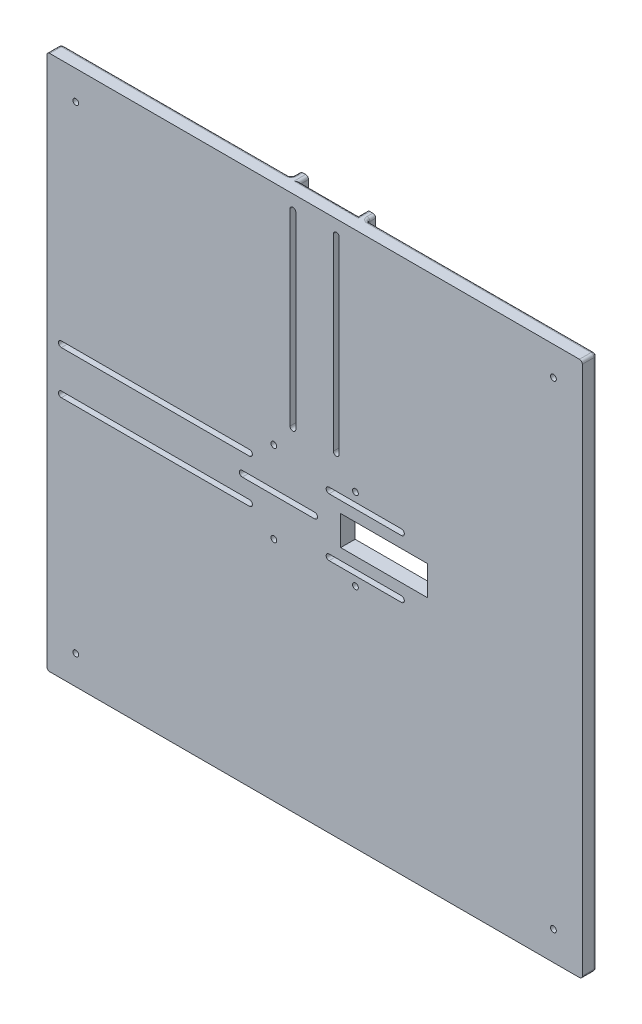
SolidWorks part; units mm, degrees
ref_plane "Plan de face" through (0, 0, 0) normal (0, 0, 1) x (1, 0, 0)
ref_plane "Plan de dessus" through (0, 0, 0) normal (0, 1, 0) x (1, 0, 0)
ref_plane "Plan de droite" through (0, 0, 0) normal (1, 0, 0) x (0, 0, -1)
sketch "Esquisse1" plane through (0, 0, 0) normal (0, 0, 1) x (1, 0, 0)
  line L1 (-92.5, 92.5) -> (92.5, 92.5)
  line L2 (-92.5, 92.5) -> (-92.5, -92.5)
  line L3 (-92.5, -92.5) -> (92.5, -92.5)
  line L4 (92.5, 92.5) -> (92.5, -92.5)
  dimension "D1" = 185
  dimension "D2" = 185
  dimension "D3" = 92.5
  dimension "D4" = 92.5
extrude "Boss.-Extru.1" add sketch "Esquisse1" along normal blind 5
sketch "Esquisse2" plane through (0, 0, 0) normal (0, 0, -1) x (-1, 0, 0)
  line L1 (22.5, 10.1) -> (92.5, 10.1)
  line L4 (92.5, 10.1) -> (92.5, 13.1)
  line L5 (92.5, -13.1) -> (22.5, -13.1)
  line L6 (92.5, -13.1) -> (92.5, -10.1)
  line L7 (92.5, -10.1) -> (22.5, -10.1)
  line L19 (92.5, 92.5) -> (92.5, -92.5) construction
  line L24 (13.1, 22.5) -> (13.1, 92.5)
  line L25 (-92.5, 92.5) -> (92.5, 92.5) construction
  line L26 (10.1, 22.5) -> (10.1, 92.5)
  line L28 (-13.1, 92.5) -> (-10.1, 92.5)
  line L29 (10.1, 92.5) -> (13.1, 92.5)
  line L31 (-10.1, 92.5) -> (-10.1, 22.5)
  line L32 (-13.1, 92.5) -> (-13.1, 22.5)
  line L33 (-10.1, 22.5) -> (-13.1, 22.5)
  line L35 (22.5, -10.1) -> (22.5, -13.1)
  line L36 (92.5, 13.1) -> (22.5, 13.1)
  line L37 (22.5, 13.1) -> (22.5, 10.1)
  line L38 (13.1, 22.5) -> (10.1, 22.5)
  dimension "D1" = 20.2
  dimension "D2" = 3
  dimension "D3" = 3
  dimension "D4" = 10.1
  dimension "D5" = 3
  dimension "D6" = 3
  dimension "D7" = 20.2
  dimension "D8" = 10.1
  dimension "D9" = 70
  dimension "D10" = 70
extrude "Boss.-Extru.2" add sketch "Esquisse2" along normal blind 3
fillet "Congé1" radius 1 32 edges at (-13.1, 57.5, 0) (-57.5, -13.1, 0) (-13.1, 92.5, -1.5) (-92.5, -13.1, -1.5) (92.5, -92.5, 2.5) (92.5, 92.5, 2.5) (92.5, 0, 0) (0, 92.5, 0) (-92.5, 0, 0) (-52.8, 92.5, 0) (-92.5, 52.8, 0) (-92.5, 92.5, 2.5) (52.8, 92.5, 0) (0, -92.5, 0) (-92.5, -52.8, 0) (-92.5, -92.5, 2.5) (-10.1, 92.5, -1.5) (-92.5, 10.1, -1.5) (-92.5, -10.1, -1.5) (13.1, 92.5, -1.5) (10.1, 92.5, -1.5) (13.1, 57.5, 0) (-92.5, 13.1, -1.5) (-57.5, 13.1, 0) (-22.5, -11.6, 0) (11.6, 22.5, 0) (-11.6, 22.5, 0) (-22.5, 11.6, 0) (-22.5, -13.1, -1.5) (13.1, 22.5, -1.5) (-13.1, 22.5, -1.5) (-22.5, 13.1, -1.5)
sketch "Esquisse4" plane through (0, 0, 0) normal (0, 0, -1) x (-1, 0, 0)
  line L4 (-92.5, -91.5) -> (-92.5, 91.5) construction
  line L5 (91.5, -92.5) -> (-91.5, -92.5) construction
  line L6 (-91.5, 92.5) -> (-14.1, 92.5) construction
  line L7 (92.5, -14.1) -> (92.5, -91.5) construction
  circle A0 centre (-14.1, 14.1) radius 1
  circle A1 centre (14.1, 14.1) radius 1
  circle A2 centre (14.1, -14.1) radius 1
  circle A3 centre (-14.1, -14.1) radius 1
  circle A4 centre (-82.5, -82.5) radius 1
  circle A5 centre (-82.5, 82.5) radius 1
  circle A6 centre (82.5, -82.5) radius 1
  circle A7 centre (82.5, 82.5) radius 1
  dimension "D1" = 2
  dimension "D4" = 4
  dimension "D5" = 4
  dimension "D6" = 10
  dimension "D7" = 10
  dimension "D8" = 10
  dimension "D9" = 10
  dimension "D10" = 4
  dimension "D11" = 4
extrude "Enlèv. mat.-Extru.1" cut sketch "Esquisse4" against normal up to next
sketch "Esquisse5" plane through (0, 0, 0) normal (0, 0, -1) x (-1, 0, 0)
  line L0 (-7.5, 87.5) -> (-7.5, 22.5) construction
  line L1 (-6.5, 87.5) -> (-6.5, 22.5)
  line L2 (-8.5, 87.5) -> (-8.5, 22.5)
  line L3 (7.5, 87.5) -> (7.5, 22.5) construction
  line L4 (8.5, 87.5) -> (8.5, 22.5)
  line L5 (6.5, 87.5) -> (6.5, 22.5)
  line L9 (10.1, 91.5) -> (10.1, 21.5) construction
  line L10 (-10.1, 92.5) -> (10.1, 92.5) construction
  line L11 (-10.1, 21.5) -> (-10.1, 91.5) construction
  line L12 (-91.5, 92.5) -> (-14.1, 92.5) construction
  arc A0 (-6.5, 87.5) -> (-8.5, 87.5) centre (-7.5, 87.5) ccw
  arc A1 (-8.5, 22.5) -> (-6.5, 22.5) centre (-7.5, 22.5) ccw
  arc A2 (8.5, 87.5) -> (6.5, 87.5) centre (7.5, 87.5) ccw
  arc A3 (6.5, 22.5) -> (8.5, 22.5) centre (7.5, 22.5) ccw
  point P2 (-7.5, 55)
  point P7 (7.5, 55)
  dimension "D1" = 1
  dimension "D2" = 1
  dimension "D3" = 2.6
  dimension "D4" = 5
  dimension "D6" = 2.6
  dimension "D7" = 70
extrude "Enlèv. mat.-Extru.2" cut sketch "Esquisse5" against normal through all
sketch "Esquisse6" plane through (0, 0, 0) normal (0, 0, -1) x (-1, 0, 0)
  line L0 (87.5, -7.5) -> (22.5, -7.5) construction
  line L1 (87.5, -8.5) -> (22.5, -8.5)
  line L2 (87.5, -6.5) -> (22.5, -6.5)
  line L3 (22.5, 7.5) -> (87.5, 7.5) construction
  line L4 (22.5, 8.5) -> (87.5, 8.5)
  line L5 (22.5, 6.5) -> (87.5, 6.5)
  line L6 (91.5, -10.1) -> (21.5, -10.1) construction
  line L7 (21.5, 10.1) -> (91.5, 10.1) construction
  line L8 (92.5, 10.1) -> (92.5, -10.1) construction
  arc A0 (87.5, -8.5) -> (87.5, -6.5) centre (87.5, -7.5) ccw
  arc A1 (22.5, -6.5) -> (22.5, -8.5) centre (22.5, -7.5) ccw
  arc A2 (22.5, 8.5) -> (22.5, 6.5) centre (22.5, 7.5) ccw
  arc A3 (87.5, 6.5) -> (87.5, 8.5) centre (87.5, 7.5) ccw
  point P2 (55, -7.5)
  point P7 (55, 7.5)
  dimension "D1" = 1
  dimension "D2" = 1
  dimension "D3" = 2.6
  dimension "D4" = 2.6
  dimension "D5" = 5
  dimension "D7" = 70
extrude "Enlèv. mat.-Extru.3" cut sketch "Esquisse6" against normal up to next
sketch "Esquisse9" plane through (0, 0, 5) normal (0, 0, 1) x (1, 0, 0)
  line L0 (-25, 0) -> (0, 0) construction
  line L1 (-25, 1) -> (0, 1)
  line L2 (-25, -1) -> (0, -1)
  line L3 (5, 10) -> (30, 10) construction
  line L4 (5, 11) -> (30, 11)
  line L5 (5, 9) -> (30, 9)
  line L6 (5, -10) -> (30, -10) construction
  line L7 (5, -9) -> (30, -9)
  line L8 (5, -11) -> (30, -11)
  arc A0 (-25, 1) -> (-25, -1) centre (-25, 0) ccw
  arc A1 (0, -1) -> (0, 1) centre (0, 0) ccw
  arc A2 (5, 11) -> (5, 9) centre (5, 10) ccw
  arc A3 (30, 9) -> (30, 11) centre (30, 10) ccw
  arc A4 (5, -9) -> (5, -11) centre (5, -10) ccw
  arc A5 (30, -11) -> (30, -9) centre (30, -10) ccw
  point P3 (-12.5, 0)
  point P8 (17.5, 10)
  point P15 (17.5, -10)
  point P22 (0, 0)
  dimension "D4" = 25
  dimension "D5" = 30
  dimension "D1" = 2
  dimension "D2" = 2
  dimension "D3" = 2
  dimension "D6" = 25
  dimension "D7" = 10
  dimension "D8" = 10
  dimension "D9" = 25
extrude "Enlèv. mat.-Extru.5" cut sketch "Esquisse9" against normal up to next
sketch "Esquisse11" plane through (0, 0, 0) normal (0, 0, -1) x (-1, 0, 0)
  line L1 (-9, 5.1) -> (-39, 5.1)
  line L2 (-9, 5.1) -> (-9, -5.1)
  line L3 (-9, -5.1) -> (-39, -5.1)
  line L4 (-39, 5.1) -> (-39, -5.1)
  dimension "D1" = 9
  dimension "D2" = 10.2
  dimension "D3" = 5.1
  dimension "D4" = 30
extrude "Enlèv. mat.-Extru.7" cut sketch "Esquisse11" against normal up to next
sketch "Esquisse12" plane through (0, 0, 0) normal (0, 0, -1) x (-1, 0, 0)
  line L1 (-33, 12.1) -> (-2, 12.1)
  line L2 (-33, 12.1) -> (-33, 7.9)
  line L3 (-33, 7.9) -> (-2, 7.9)
  line L4 (-2, 12.1) -> (-2, 7.9)
  line L5 (-33, -7.9) -> (-2, -7.9)
  line L6 (-33, -7.9) -> (-33, -12.1)
  line L7 (-33, -12.1) -> (-2, -12.1)
  line L8 (-2, -7.9) -> (-2, -12.1)
  line L9 (-3, 2.1) -> (28, 2.1)
  line L10 (-3, 2.1) -> (-3, -2.1)
  line L11 (-3, -2.1) -> (28, -2.1)
  line L12 (28, 2.1) -> (28, -2.1)
  arc A0 (-30, 11) -> (-30, 9) centre (-30, 10) ccw construction
  arc A1 (-30, -9) -> (-30, -11) centre (-30, -10) ccw construction
  arc A2 (-5, -11) -> (-5, -9) centre (-5, -10) ccw construction
  arc A3 (0, 1) -> (0, -1) centre (0, 0) ccw construction
  arc A4 (25, -1) -> (25, 1) centre (25, 0) ccw construction
  arc A5 (-5, 9) -> (-5, 11) centre (-5, 10) ccw construction
  point P15 (-31, 10)
  point P20 (-31, -10)
  dimension "D7" = 3
  dimension "D8" = 3
  dimension "D9" = 3
  dimension "D10" = 3
  dimension "D11" = 3
  dimension "D12" = 3
  dimension "D1" = 2.1
  dimension "D2" = 4.2
  dimension "D3" = 2.1
  dimension "D4" = 4.2
  dimension "D5" = 2.1
  dimension "D6" = 4.2
extrude "Enlèv. mat.-Extru.9" cut sketch "Esquisse12" against normal blind 2
fillet "Congé2" radius 0.5 11 edges at (33, -12.1, 1) (33, -7.9, 1) (2, -7.9, 1) (2, -12.1, 1) (-28, -2.1, 1) (-28, 2.1, 1) (3, -2.1, 1) (3, 2.1, 1) (2, 12.1, 1) (33, 7.9, 1) (33, 12.1, 1)
sketch "Esquisse13" plane through (0, 0, 0) normal (0, 0, -1) x (-1, 0, 0)
  line L0 (-14.1, 91.5) -> (-91.5, 91.5) construction
  line L1 (-80.17, -82.5) -> (-81.335, -80.4822)
  line L2 (-81.335, -80.4822) -> (-83.665, -80.4822)
  line L3 (-83.665, -80.4822) -> (-84.83, -82.5)
  line L4 (-84.83, -82.5) -> (-83.665, -84.5178)
  line L5 (-83.665, -84.5178) -> (-81.335, -84.5178)
  line L6 (-81.335, -84.5178) -> (-80.17, -82.5)
  line L7 (83.665, -84.5178) -> (84.83, -82.5)
  line L8 (84.83, -82.5) -> (83.665, -80.4822)
  line L9 (83.665, -80.4822) -> (81.335, -80.4822)
  line L10 (81.335, -80.4822) -> (80.17, -82.5)
  line L11 (80.17, -82.5) -> (81.335, -84.5178)
  line L12 (81.335, -84.5178) -> (83.665, -84.5178)
  line L13 (84.83, 82.5) -> (83.665, 84.5178)
  line L14 (83.665, 84.5178) -> (81.335, 84.5178)
  line L15 (81.335, 84.5178) -> (80.17, 82.5)
  line L16 (80.17, 82.5) -> (81.335, 80.4822)
  line L17 (81.335, 80.4822) -> (83.665, 80.4822)
  line L18 (83.665, 80.4822) -> (84.83, 82.5)
  line L19 (-80.17, 82.5) -> (-81.335, 84.5178)
  line L20 (-81.335, 84.5178) -> (-83.665, 84.5178)
  line L21 (-83.665, 84.5178) -> (-84.83, 82.5)
  line L22 (-84.83, 82.5) -> (-83.665, 80.4822)
  line L23 (-83.665, 80.4822) -> (-81.335, 80.4822)
  line L24 (-81.335, 80.4822) -> (-80.17, 82.5)
  line L25 (91.5, 91.5) -> (14.1, 91.5) construction
  line L26 (-91.5, -91.5) -> (91.5, -91.5) construction
  circle A0 centre (-82.5, -82.5) radius 2.0178 construction
  circle A1 centre (82.5, -82.5) radius 2.0178 construction
  circle A2 centre (82.5, 82.5) radius 2.0178 construction
  circle A3 centre (-82.5, 82.5) radius 2.0178 construction
  dimension "D1" = 2.33
  dimension "D2" = 2.33
  dimension "D3" = 2.33
  dimension "D4" = 2.33
extrude "Enlèv. mat.-Extru.10" cut sketch "Esquisse13" against normal blind 2
